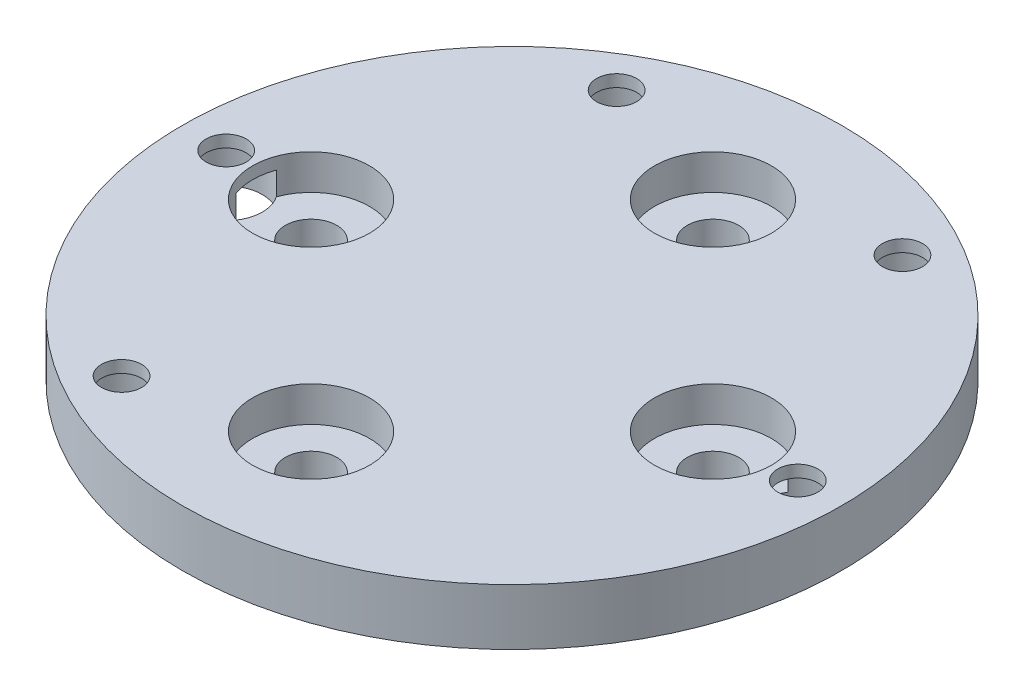
SolidWorks part; units mm, degrees
ref_plane "Front Plane" through (0, 0, 0) normal (0, 0, 1) x (1, 0, 0)
ref_plane "Top Plane" through (0, 0, 0) normal (0, 1, 0) x (1, 0, 0)
ref_plane "Right Plane" through (0, 0, 0) normal (1, 0, 0) x (0, 0, -1)
sketch "Sketch1" plane through (0, 0, 0) normal (0, 1, 0) x (1, 0, 0)
  circle A0 centre (0, 0) radius 41
  dimension "D1" = 82
extrude "Boss-Extrude1" add sketch "Sketch1" along normal blind 7
sketch "Sketch3" plane through (0, 7, 0) normal (0, 1, 0) x (1, 0, 0)
  line L0 (0, 0) -> (0, 25) construction
  line L1 (0, 0) -> (-7.0711, 7.0711) construction
  line L2 (-28.9914, -28.9914) -> (28.9914, 28.9914) construction
  line L3 (0, 0) -> (7.0711, -7.0711) construction
  line L4 (0, 41) -> (0, -41) construction
  circle A0 centre (0, 0) radius 41 construction
  circle A1 centre (-7.0711, 7.0711) radius 2.6
  circle A2 centre (7.0711, -7.0711) radius 2.6
  point P4 (0, 25)
  point P10 (0, 0)
  point P13 (0, 0)
  dimension "D4" = 5.2
  dimension "D1" = 25
  dimension "D2" = 10
  dimension "D3" = 45
hole_wizard "CBORE for M6 Hex Head Bolt1" positions "Sketch7" profile "Sketch8" counterbore size "M6" standard "ANSI Metric" end condition through all
sketch "Sketch7" plane through (0, 7, 0) normal (0, 1, 0) x (1, 0, 0)
  point P0 (0, 25)
sketch "Sketch8" plane through (0, 7, -25) normal (1, 0, 0) x (0, 0, 1)
  line L0 (0, 0) -> (0, 7)
  line L1 (0, 7) -> (3.2, 7)
  line L3 (3.2, 7) -> (3.2, 4.38)
  line L4 (3.2, 4.38) -> (7.275, 4.38)
  line L5 (7.275, 4.38) -> (7.275, 0)
  line L7 (7.275, 0) -> (0, 0)
  line L11 (0, -6.35) -> (0, 107.95) construction
  dimension "Thru Hole Dia." = 6.4
  dimension "Thru Hole Depth" = 7
  dimension "C'Bore Dia." = 14.55
  dimension "C'Bore Depth" = 4.38
pattern_circular "CirPattern2" count 4 over 360 about axis through (0, 0, 0) along (0, 1, 0) of "CBORE for M6 Hex Head Bolt1"
sketch "Sketch9" plane through (0, 7, 0) normal (0, 1, 0) x (1, 0, 0)
  line L0 (0, 41) -> (0, -41) construction
  line L1 (0, 0) -> (-10, 0) construction
  circle A0 centre (0, 0) radius 41 construction
  circle A1 centre (-10, 0) radius 2.6
  circle A4 centre (10, 0) radius 2.6
  dimension "D2" = 5.2
  dimension "D1" = 10
extrude "Cut-Extrude2" [suppressed] cut sketch "Sketch9" against normal blind 5.5
sketch "Sketch13" plane through (0, 0, 0) normal (0, -1, 0) x (1, 0, 0)
  line L0 (25.4558, 25.4558) -> (28.9914, 28.9914) construction
  line L1 (-41, 0) -> (41, 0) construction
  line L2 (0, 25) -> (0, 41) construction
  line L3 (0, 0) -> (9.3175, 34.7733)
  line L4 (0, 0) -> (25.4558, 25.4558) construction
  line L5 (0, 0) -> (34.7733, 9.3175)
  arc A0 (34.7733, 9.3175) -> (9.3175, 34.7733) centre (0, 0) ccw
  arc A1 (20.7674, 5.5646) -> (5.5646, 20.7674) centre (0, 0) ccw
  circle A2 centre (0, 0) radius 41 construction
  dimension "D1" = 5
  dimension "D2" = 16
  dimension "D3" = 135
  dimension "D4" = 30
extrude "Cut-Extrude3" [suppressed] cut sketch "Sketch13" against normal blind 3 contours A1 L5 A0 L3
sketch "Sketch15" plane through (0, 0, 0) normal (0, -1, 0) x (1, 0, 0)
  circle A0 centre (35.56, 0) radius 2.5 construction
  circle A1 centre (17.78, -30.7959) radius 2.5 construction
  circle A2 centre (-17.78, -30.7959) radius 2.5 construction
  circle A3 centre (-35.56, 0) radius 2.5 construction
  circle A5 centre (-17.78, 30.7959) radius 2.5 construction
  circle A6 centre (35.56, 0) radius 2.5
  circle A7 centre (17.78, -30.7959) radius 2.5
  circle A8 centre (-17.78, -30.7959) radius 2.5
  circle A9 centre (-35.56, 0) radius 2.5
  circle A11 centre (-17.78, 30.7959) radius 2.5
extrude "Cut-Extrude4" cut sketch "Sketch15" along normal through all from surface at -7 starting at face at (25, 7, 7.275)
sketch "Sketch16" plane through (0, 0, 0) normal (0, -1, 0) x (1, 0, 0)
  circle A0 centre (-17.78, 30.7959) radius 2.5 construction
  circle A2 centre (35.56, 0) radius 2.5 construction
  circle A3 centre (17.78, -30.7959) radius 2.5 construction
  circle A4 centre (-35.56, 0) radius 2.5 construction
  circle A5 centre (-17.78, -30.7959) radius 2.5 construction
  circle A6 centre (-17.78, 30.7959) radius 2.5 construction
  circle A8 centre (35.56, 0) radius 2.5 construction
  circle A9 centre (17.78, -30.7959) radius 2.5 construction
  circle A10 centre (-35.56, 0) radius 2.5 construction
  circle A11 centre (-17.78, -30.7959) radius 2.5 construction
  circle A12 centre (-17.78, 30.7959) radius 4.5
  circle A13 centre (-35.56, 0) radius 4.5
  circle A14 centre (35.56, 0) radius 4.5
  circle A15 centre (-17.78, -30.7959) radius 4.5
  circle A16 centre (17.78, -30.7959) radius 4.5
  dimension "D1" = 9
extrude "Cut-Extrude5" cut sketch "Sketch16" against normal blind 5.5
sketch "Sketch17" plane through (0, 0, 0) normal (0, -1, 0) x (1, 0, 0)
  circle A0 centre (0, 0) radius 30
  circle A1 centre (35.56, 0) radius 4.5 construction
  circle A2 centre (25, 0) radius 3.2 construction
  circle A3 centre (35.56, 0) radius 4.5 construction
  circle A4 centre (25, 0) radius 3.2
  circle A6 centre (0, 25) radius 3.2 construction
  circle A7 centre (-25, 0) radius 3.2 construction
  circle A8 centre (0, -25) radius 3.2 construction
  circle A9 centre (0, -25) radius 3.2
  circle A10 centre (-25, 0) radius 3.2
  circle A11 centre (0, 25) radius 3.2
  point P1 (8.4674, 28.9778)
  dimension "D1" = 60
extrude "Boss-Extrude2" add sketch "Sketch17" along normal blind 7
